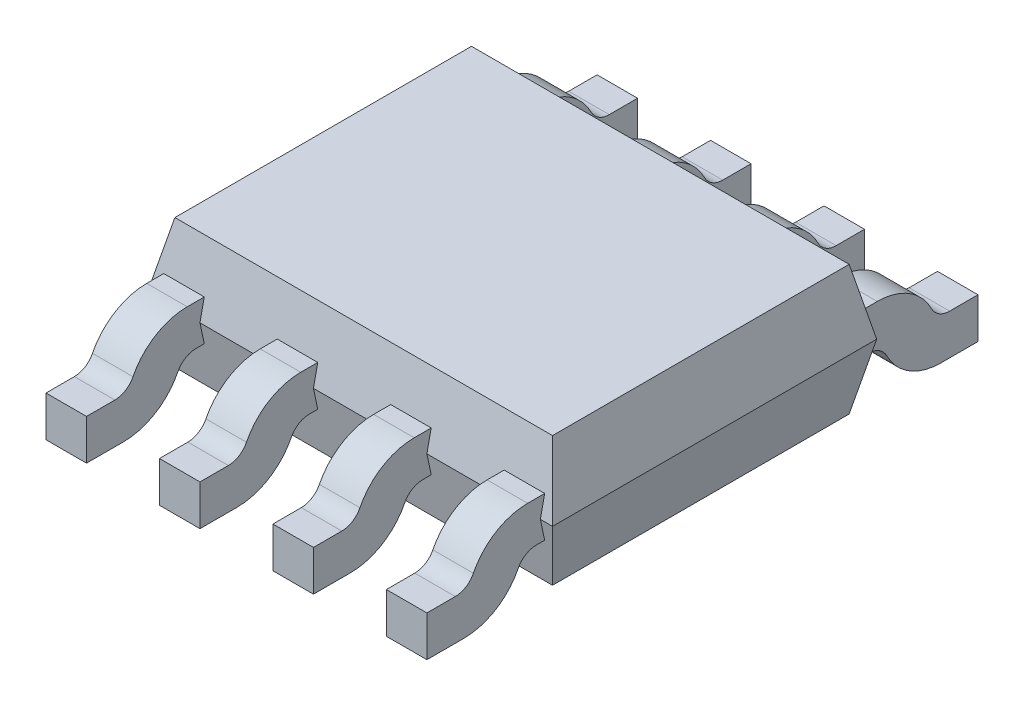
SolidWorks part; units mm, degrees
ref_plane "Front Plane" through (0, 0, 0) normal (0, 0, 1) x (1, 0, 0)
ref_plane "Top Plane" through (0, 0, 0) normal (0, 1, 0) x (1, 0, 0)
ref_plane "Right Plane" through (0, 0, 0) normal (1, 0, 0) x (0, 0, -1)
sketch "Sketch1" plane through (0, 0, 0) normal (0, 1, 0) x (1, 0, 0)
  line L1 (-2.5, 2) -> (2.5, 2)
  line L2 (-2.5, 2) -> (-2.5, -2)
  line L3 (-2.5, -2) -> (2.5, -2)
  line L4 (2.5, 2) -> (2.5, -2)
  line L5 (-2.5, 2) -> (2.5, -2) construction
  line L6 (-2.5, -2) -> (2.5, 2) construction
  point P0 (0, 0)
  dimension "D1" = 5
  dimension "D2" = 4
extrude "Boss-Extrude1" add sketch "Sketch1" along normal mid plane 1.6 draft 12
ref_plane "LEG REFERENCE PLANE" through (0, 0, 2) normal (0, 0, 1) x (1, 0, 0)
sketch "Sketch2" plane through (0, 0, 2) normal (0, 0, 1) x (1, 0, 0)
  line L0 (-2.5, 0) -> (2.5, 0) construction
  line L1 (1.85, 0.25) -> (2.35, 0.25)
  line L2 (1.85, 0.25) -> (1.85, -0.25)
  line L3 (1.85, -0.25) -> (2.35, -0.25)
  line L4 (2.35, 0.25) -> (2.35, -0.25)
  line L5 (1.85, 0.25) -> (2.35, -0.25) construction
  line L6 (1.85, -0.25) -> (2.35, 0.25) construction
  point P0 (2.1, 0)
  dimension "D1" = 0.5
  dimension "D2" = 0.15
  dimension "D3" = 0.5
extrude "Boss-Extrude3" add sketch "Sketch2" along normal blind 0.8 and the other way blind 1 separate body
sketch "Sketch3" plane through (0, -0.25, 0) normal (0, -1, 0) x (-1, 0, 0)
  line L0 (-1.85, -1) -> (-1.85, -2.8) construction
  line L1 (-2.35, -2.8) -> (-1.85, -2.8)
  line L2 (-2.35, -2.8) -> (-2.35, -2.3)
  line L3 (-2.35, -2.3) -> (-1.85, -2.3)
  line L4 (-1.85, -2.8) -> (-1.85, -2.3)
  dimension "D1" = 0.5
extrude "Boss-Extrude4" add sketch "Sketch3" along normal up to surface (0.55 mm away) up to face at (0, -0.8, 0)
sketch "Sketch4" plane through (0, 0, 2.8) normal (0, 0, 1) x (1, 0, 0)
  line L0 (1.85, 0.25) -> (1.85, -0.8) construction
  line L1 (2.35, -0.8) -> (1.85, -0.8)
  line L2 (2.35, -0.8) -> (2.35, -0.3)
  line L3 (2.35, -0.3) -> (1.85, -0.3)
  line L4 (1.85, -0.8) -> (1.85, -0.3)
  dimension "D1" = 0.5
extrude "Boss-Extrude5" add sketch "Sketch4" along normal blind 0.6
fillet "Fillet1" radius 0.25 2 edges at (2.1, -0.3, 2.8) (2.1, -0.25, 2.3)
fillet "Fillet2" radius 0.75 2 edges at (2.1, -0.8, 2.3) (2.1, 0.25, 2.8)
pattern_linear "LPattern2" count 4 spacing 1.4 along (-1, 0, 0) of bodies 104
mirror "Mirror2" about plane through (0, 0, 0) normal (0, 0, 1) of bodies 104 105 106 107 111 108 109 110 112 113
